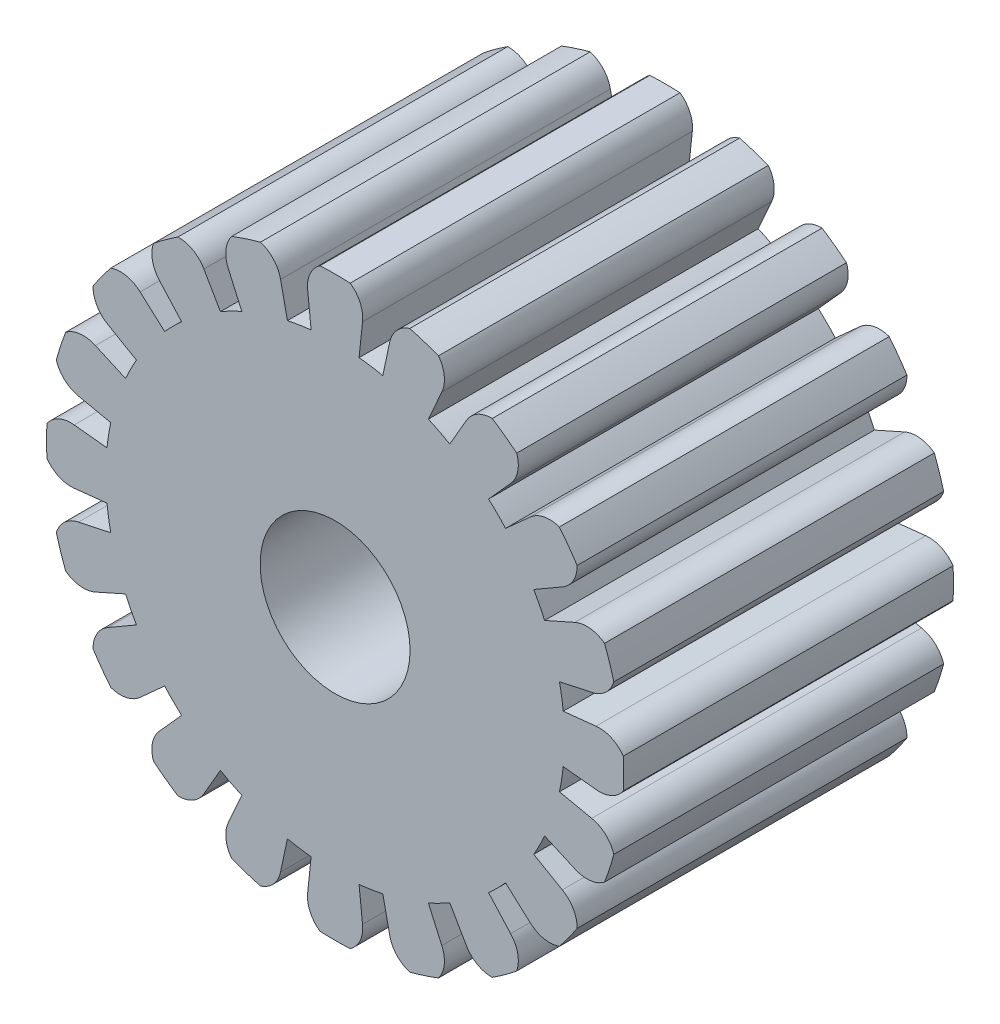
SolidWorks part; units mm, degrees
ref_plane "Front Plane" through (0, 0, 0) normal (0, 0, 1) x (1, 0, 0)
ref_plane "Top Plane" through (0, 0, 0) normal (0, 1, 0) x (1, 0, 0)
ref_plane "Right Plane" through (0, 0, 0) normal (1, 0, 0) x (0, 0, -1)
sketch "Sketch1" plane through (0, 0, 0) normal (0, 0, 1) x (1, 0, 0)
  line L2 (30.4324, 3.1986) -> (34.8083, 3.6585) construction
  line L3 (0, 0) -> (30.2233, 4.7869) construction
  line L4 (34.8083, 3.6585) -> (30.4324, 3.1986)
  line L5 (34.8083, -3.6585) -> (30.4324, -3.1986)
  line L6 (0, 0) -> (30.2233, 4.7869)
  line L7 (0, 0) -> (30.2233, -4.7869)
  arc A0 (30.2233, -4.7869) -> (30.4324, -3.1986) centre (0, 0) ccw construction
  arc A2 (38.4472, -2.0149) -> (38.4472, 2.0149) centre (0, 0) ccw construction
  arc A3 (30.2233, 4.7869) -> (30.4324, 3.1986) centre (0, 0) cw
  arc A4 (38.4472, 2.0149) -> (38.4472, -2.0149) centre (0, 0) cw
  arc A5 (34.8083, 3.6585) -> (38.4472, 2.0149) centre (35.2567, -0.1989) cw
  arc A6 (34.8083, -3.6585) -> (38.4472, -2.0149) centre (35.2567, 0.1989) ccw
  arc A7 (30.2233, -4.7869) -> (30.4324, -3.1986) centre (0, 0) ccw
  arc A8 (30.4324, 3.1986) -> (30.2233, 4.7869) centre (0, 0) ccw construction
  dimension "D2" = 77
  dimension "D3" = 61.2
  dimension "D6" = 3
extrude "Boss-Extrude3" add sketch "Sketch1" along normal mid plane 44
pattern_circular "CirPattern3" count 20 over 360 about axis through (0, 0, 0) along (0, 0, 1) of "Boss-Extrude3"
sketch "Sketch2" plane through (0, 0, 0) normal (0, 0, 1) x (1, 0, 0)
  circle A0 centre (0, 0) radius 10
  dimension "D1" = 20
extrude "Cut-Extrude1" cut sketch "Sketch2" against normal through all both and the other way through all
sketch "Sketch3" plane through (0, 0, 0) normal (0, 0, 1) x (1, 0, 0)
  circle A1 centre (0, 0) radius 35 construction
  dimension "D1" = 70
